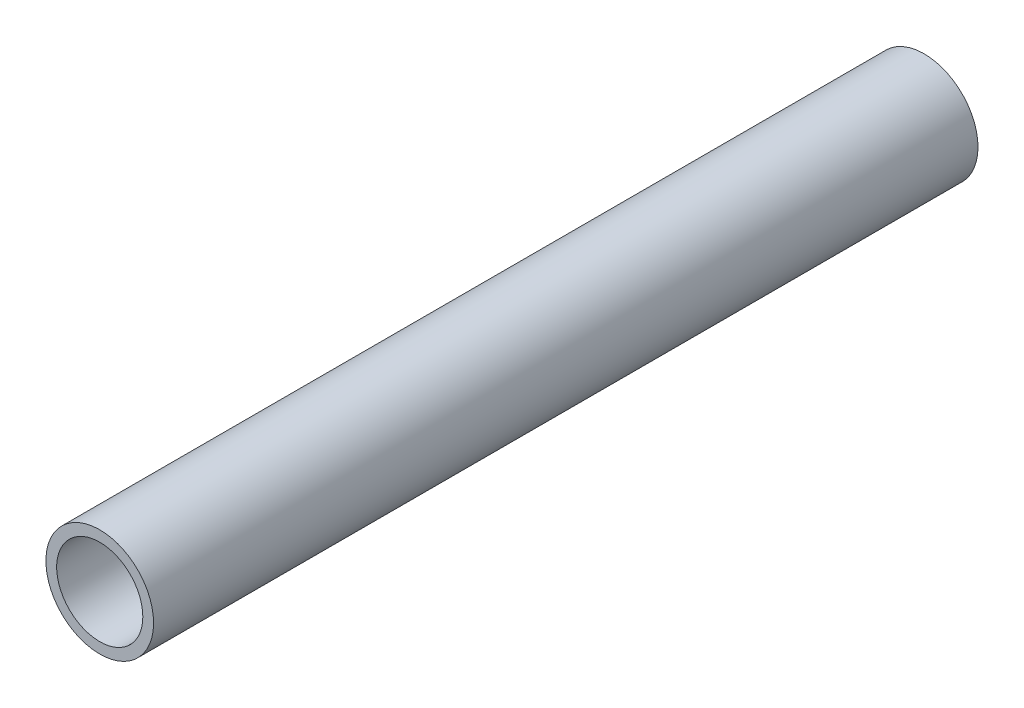
SolidWorks part; units mm, degrees
ref_plane "Front Plane" through (0, 0, 0) normal (0, 0, 1) x (1, 0, 0)
ref_plane "Top Plane" through (0, 0, 0) normal (0, 1, 0) x (1, 0, 0)
ref_plane "Right Plane" through (0, 0, 0) normal (1, 0, 0) x (0, 0, -1)
sketch "Sketch1" plane through (0, 0, 0) normal (0, 0, 1) x (1, 0, 0)
  circle A0 centre (0, 0) radius 1.25
  circle A1 centre (0, 0) radius 1
extrude "Boss-Extrude1" add sketch "Sketch1" along normal blind 19.14
equation "\"D1@Boss-Extrude1\" = \"HL@parametersSketch@prostheticParameters.SLDPRT\" * 0.244 - 4 - 12 - 10'Ring PIP Tube"
